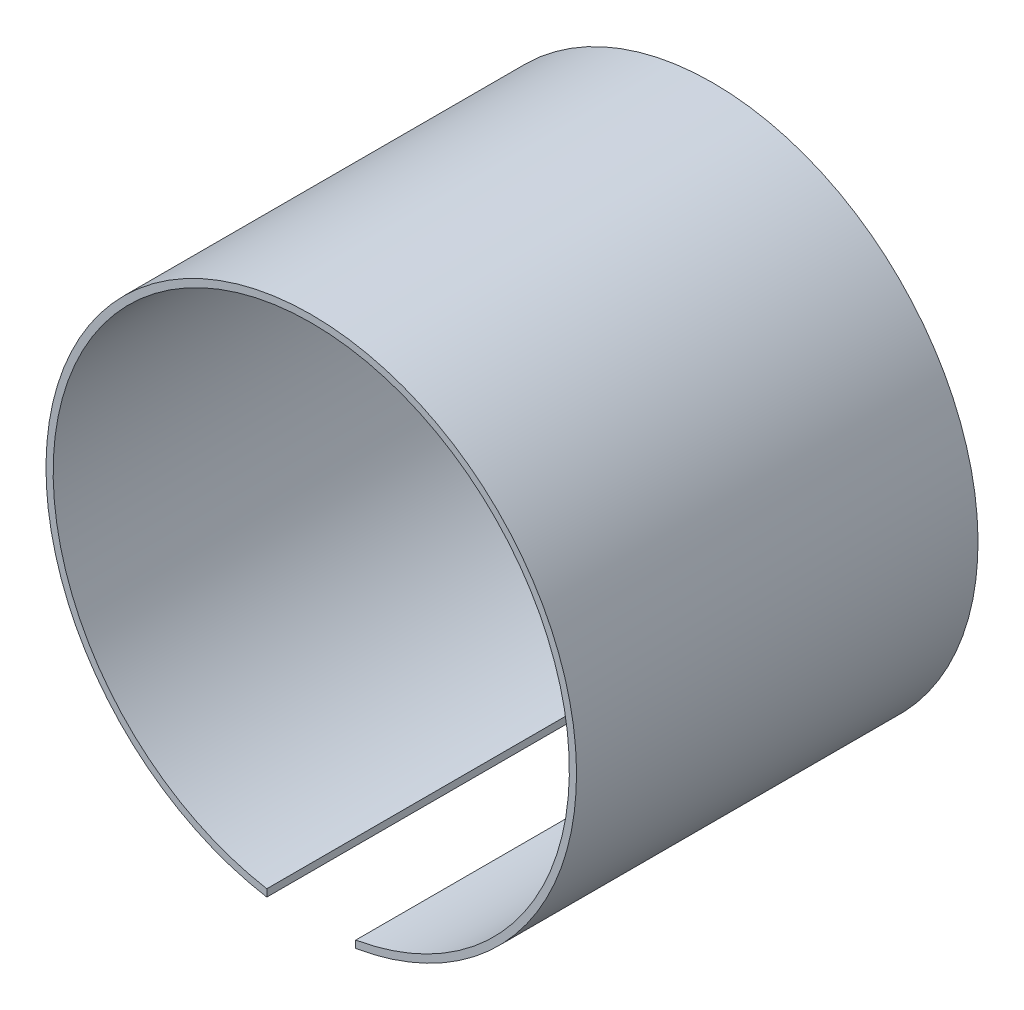
SolidWorks part; units mm, degrees
ref_plane "Alzado" through (0, 0, 0) normal (0, 0, 1) x (1, 0, 0)
ref_plane "Planta" through (0, 0, 0) normal (0, 1, 0) x (1, 0, 0)
ref_plane "Vista lateral" through (0, 0, 0) normal (1, 0, 0) x (0, 0, -1)
sketch "Croquis1" plane through (0, 0, 0) normal (0, 0, 1) x (1, 0, 0)
  line L0 (0, 0) -> (-3.1, 0) construction
  line L1 (-3.1, 0) -> (-3.1, -17.731) construction
  line L2 (0, 0) -> (3.1, 0) construction
  line L3 (3.1, 0) -> (3.1, -17.731) construction
  line L4 (-3.1, -17.731) -> (-3.1, -18.2384)
  line L5 (3.1, -17.731) -> (3.1, -18.2384)
  arc A0 (3.1, -17.731) -> (-3.1, -17.731) centre (0, 0) ccw
  arc A1 (3.1, -18.2384) -> (-3.1, -18.2384) centre (0, 0) ccw
  dimension "D1" = 36
  dimension "D2" = 37
  dimension "D3" = 3.1
  dimension "D4" = 3.1
extrude "Saliente-Extruir1" add sketch "Croquis1" along normal blind 28
